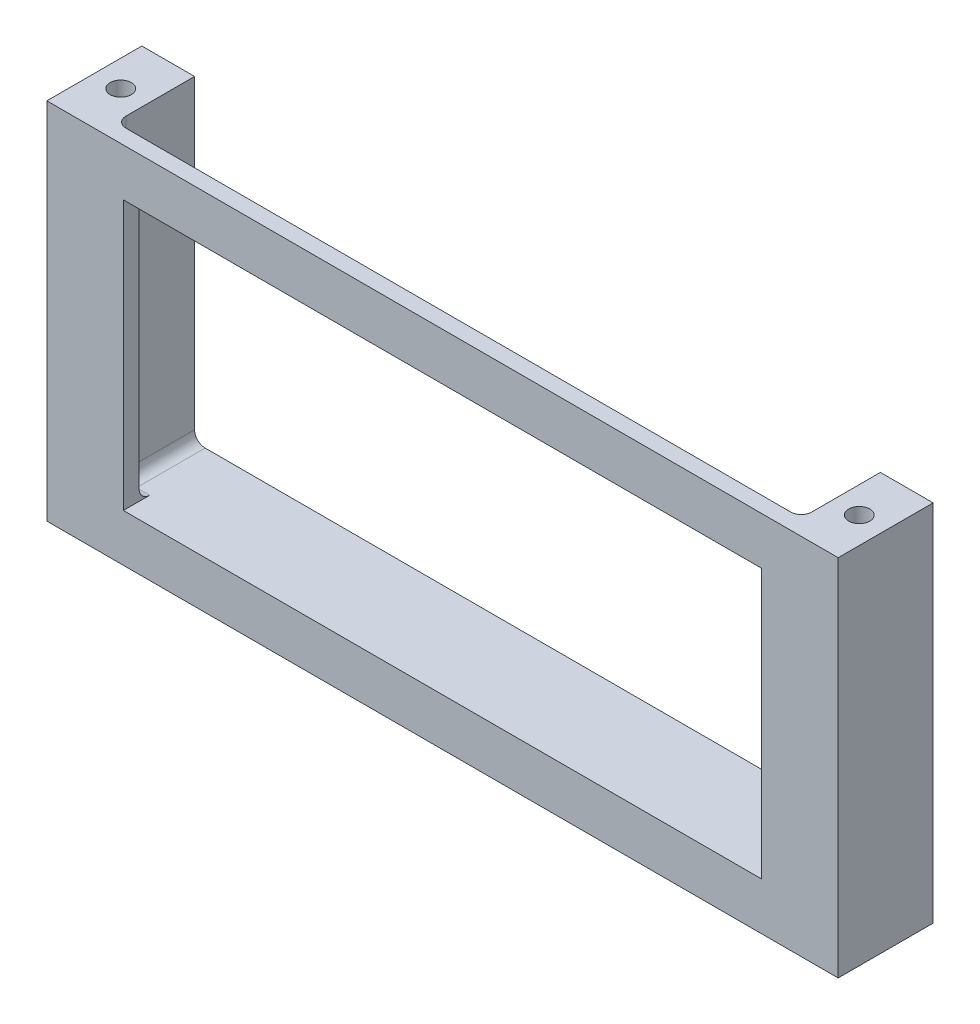
SolidWorks part; units mm, degrees
ref_plane "Front Plane" through (0, 0, 0) normal (0, 0, 1) x (1, 0, 0)
ref_plane "Top Plane" through (0, 0, 0) normal (0, 1, 0) x (1, 0, 0)
ref_plane "Right Plane" through (0, 0, 0) normal (1, 0, 0) x (0, 0, -1)
sketch "Sketch1" plane through (0, 0, 0) normal (0, 1, 0) x (1, 0, 0)
  line L1 (65, 1.5) -> (-65, 1.5)
  line L2 (65, 1.5) -> (65, -1.5)
  line L3 (65, -1.5) -> (-65, -1.5)
  line L4 (-65, 1.5) -> (-65, -1.5)
  line L5 (65, 1.5) -> (-65, -1.5) construction
  line L6 (65, -1.5) -> (-65, 1.5) construction
  point P0 (0, 0)
  dimension "D1" = 130
  dimension "D2" = 3
extrude "Boss-Extrude1" add sketch "Sketch1" along normal blind 69
sketch "Sketch2" plane through (0, 0, 1.5) normal (0, 0, 1) x (1, 0, 0)
  line L0 (-65, 34.5) -> (0, 34.5) construction
  line L5 (-65, 69) -> (-65, 0) construction
  line L6 (0, 34.5) -> (0, 0) construction
  line L7 (-65, 0) -> (65, 0) construction
  line L9 (60.5, 60) -> (-60.5, 60)
  line L10 (60.5, 60) -> (60.5, 9)
  line L11 (60.5, 9) -> (-60.5, 9)
  line L12 (-60.5, 60) -> (-60.5, 9)
  line L13 (60.5, 60) -> (-60.5, 9) construction
  line L14 (60.5, 9) -> (-60.5, 60) construction
  dimension "D1" = 121
  dimension "D2" = 51
extrude "Cut-Extrude1" cut sketch "Sketch2" against normal blind 65
sketch "Sketch3" plane through (0, 0, -1.5) normal (0, 0, -1) x (-1, 0, 0)
  line L0 (75, 0) -> (-75, 0)
  line L1 (-75, 0) -> (-75, 69)
  line L2 (-75, 69) -> (-65, 69)
  line L3 (-65, 69) -> (-65, 9)
  line L4 (-65, 9) -> (65, 9)
  line L5 (65, 9) -> (65, 69)
  line L6 (65, 69) -> (75, 69)
  line L7 (75, 69) -> (75, 0)
  line L8 (-65, 69) -> (-65, 0) construction
  line L9 (65, 69) -> (65, 0) construction
  line L10 (60.5, 9) -> (-60.5, 9) construction
  dimension "D1" = 69
  dimension "D3" = 10
extrude "Boss-Extrude3" add sketch "Sketch3" along normal blind 15 and the other way blind 3
sketch "Sketch4" plane through (0, 69, 0) normal (0, 1, 0) x (1, 0, 0)
  line L0 (0, -10.6315) -> (0, 38.8318) construction
  line L1 (-70, 16.5) -> (-70, 7.5) construction
  line L2 (-75, 7.5) -> (75, 7.5) construction
  line L3 (-75, -1.5) -> (-75, 16.5) construction
  line L4 (75, -1.5) -> (75, 16.5) construction
  line L5 (-75, 16.5) -> (-65, 16.5) construction
  circle A0 centre (-70, 7.5) radius 2
  circle A1 centre (70, 7.5) radius 2
  dimension "D1" = 4
extrude "Cut-Extrude2" cut sketch "Sketch4" against normal through all
fillet "Fillet1" radius 2 2 edges at (65, 9, -9) (-65, 9, -9)
fillet "Fillet2" radius 2 6 edges at (-64.4142, 9.5858, -1.5) (64.4142, 9.5858, -1.5) (-65, 40, -1.5) (65, 40, -1.5) (-61.75, 9, -1.5) (61.75, 9, -1.5)
